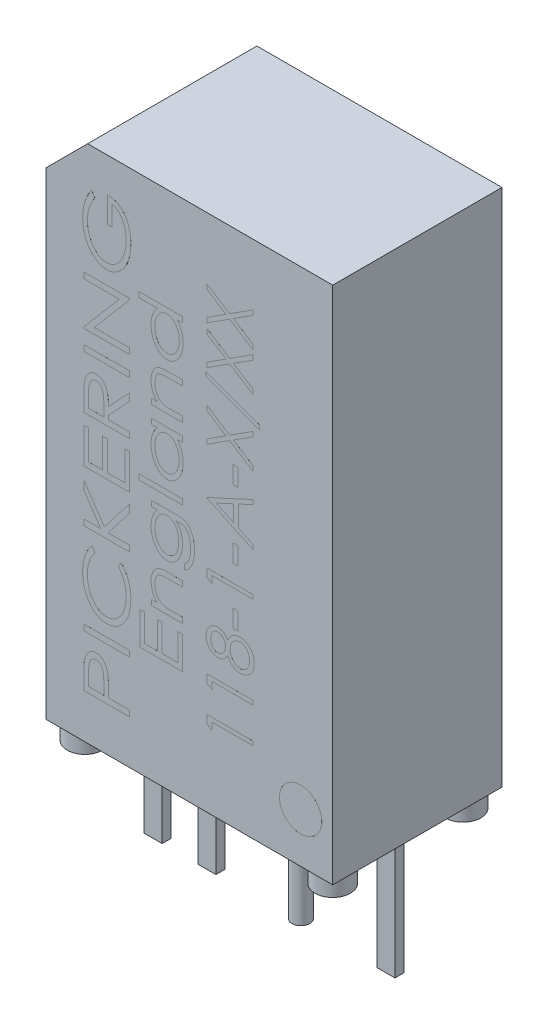
SolidWorks part; units mm, degrees
ref_plane "Front Plane" through (0, 0, 0) normal (0, 0, 1) x (1, 0, 0)
ref_plane "Top Plane" through (0, 0, 0) normal (0, 1, 0) x (1, 0, 0)
ref_plane "Right Plane" through (0, 0, 0) normal (1, 0, 0) x (0, 0, -1)
sketch "Sketch1" plane through (0, 0, 0) normal (0, 1, 0) x (1, 0, 0)
  line L1 (4.065, -2.4) -> (-4.065, -2.4)
  line L2 (4.065, -2.4) -> (4.065, 2.4)
  line L3 (4.065, 2.4) -> (-4.065, 2.4)
  line L4 (-4.065, -2.4) -> (-4.065, 2.4)
  line L5 (4.065, -2.4) -> (-4.065, 2.4) construction
  line L6 (4.065, 2.4) -> (-4.065, -2.4) construction
  point P0 (0, 0)
  dimension "D1" = 4.8
  dimension "D2" = 8.13
extrude "Main Body" add sketch "Sketch1" along normal blind 14.732
sketch "Sketch2" plane through (0, 0, 2.4) normal (0, 0, 1) x (1, 0, 0)
  line L0 (-2.885, 14.732) -> (-4.065, 13.552)
  line L1 (-4.065, 14.732) -> (4.065, 14.732) construction
  line L2 (-4.065, 14.732) -> (-4.065, 0) construction
  line L3 (-4.065, 13.552) -> (-4.065, 14.732)
  line L4 (-4.065, 14.732) -> (-2.885, 14.732)
  dimension "D1" = 6.95
  dimension "D2" = 45
extrude "Aesthetic cut" cut sketch "Sketch2" against normal through all
sketch "Sketch3" plane through (0, 0, 0) normal (0, -1, 0) x (1, 0, 0)
  line L0 (-4.065, 2.4) -> (4.065, 2.4) construction
  line L1 (-4.065, -2.4) -> (-4.065, 2.4) construction
  line L2 (4.065, -2.4) -> (-4.065, -2.4) construction
  line L3 (4.065, 2.4) -> (4.065, -2.4) construction
  circle A0 centre (-3.515, 1.85) radius 0.5
  circle A1 centre (-3.515, -1.85) radius 0.5
  circle A2 centre (3.515, 1.85) radius 0.5
  circle A3 centre (3.515, -1.85) radius 0.5
  dimension "D1" = 1
  dimension "D4" = 1
  dimension "D7" = 1
  dimension "D10" = 1
  dimension "D2" = 0.55
  dimension "D3" = 0.55
  dimension "D5" = 0.55
  dimension "D6" = 0.55
  dimension "D8" = 0.55
  dimension "D9" = 0.55
  dimension "D11" = 0.55
  dimension "D12" = 0.55
extrude "Feet" add sketch "Sketch3" along normal blind 0.508
sketch "Sketch4" plane through (0, 0, 0) normal (0, -1, 0) x (1, 0, 0)
  line L0 (-4.065, -2.4) -> (-4.065, 2.4) construction
  line L1 (-3.554, -0.127) -> (-3.046, -0.127)
  line L2 (-3.554, -0.127) -> (-3.554, 0.127)
  line L3 (-3.554, 0.127) -> (-3.046, 0.127)
  line L4 (-3.046, -0.127) -> (-3.046, 0.127)
  line L5 (-3.554, -0.127) -> (-3.046, 0.127) construction
  line L6 (-3.554, 0.127) -> (-3.046, -0.127) construction
  line L13 (-2.03, -0.127) -> (-1.522, -0.127)
  line L14 (-2.03, -0.127) -> (-2.03, 0.127)
  line L15 (-2.03, 0.127) -> (-1.522, 0.127)
  line L16 (-1.522, -0.127) -> (-1.522, 0.127)
  line L17 (-2.03, -0.127) -> (-1.522, 0.127) construction
  line L18 (-2.03, 0.127) -> (-1.522, -0.127) construction
  line L19 (3.05, -0.127) -> (3.558, -0.127)
  line L20 (3.05, -0.127) -> (3.05, 0.127)
  line L21 (3.05, 0.127) -> (3.558, 0.127)
  line L22 (3.558, -0.127) -> (3.558, 0.127)
  line L23 (3.05, -0.127) -> (3.558, 0.127) construction
  line L24 (3.05, 0.127) -> (3.558, -0.127) construction
  circle A0 centre (0.764, 0) radius 0.25
  point P0 (-3.3, 0)
  point P10 (-1.776, 0)
  point P15 (3.304, 0)
  dimension "D3" = 1.524
  dimension "D4" = 0.5
  dimension "D1" = 0.508
  dimension "D2" = 0.254
  dimension "D5" = 0.508
  dimension "D6" = 0.254
  dimension "D7" = 0.508
  dimension "D8" = 0.254
  dimension "D9" = 5.08
  dimension "D10" = 2.54
  dimension "D11" = 0.765
extrude "Pins" add sketch "Sketch4" along normal blind 3.678
sketch "Sketch5" plane through (0, 0, 2.4) normal (0, 0, 1) x (1, 0, 0)
  line L0 (-1.6944, 0.9898) -> (-1.6944, 13.9319) construction
  line L1 (1.8056, 0.9898) -> (1.8056, 13.9319) construction
  line L2 (-0.1944, 0.9898) -> (-0.1944, 13.9319) construction
  circle A0 centre (3.1553, 1.3988) radius 0.6
  text T0 "PICKERING" font "Century Gothic" height 1.3
  text T1 "England" font "Century Gothic" height 1.2
  text T2 "118-1-A-X/XX" font "Century Gothic" height 1.3
  dimension "D3" = 1.2
  dimension "D1" = 1.5
  dimension "D2" = 2
extrude "Lettering" add sketch "Sketch5" along normal blind 0.0001
